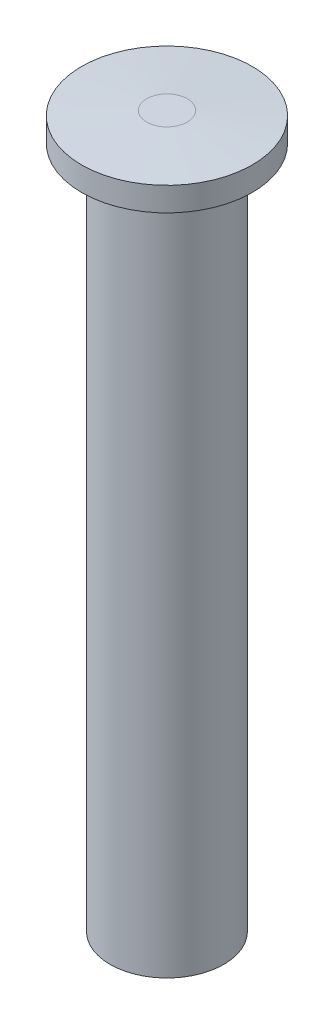
SolidWorks part; units mm, degrees
ref_plane "Front Plane" through (0, 0, 0) normal (0, 0, 1) x (1, 0, 0)
ref_plane "Top Plane" through (0, 0, 0) normal (0, 1, 0) x (1, 0, 0)
ref_plane "Right Plane" through (0, 0, 0) normal (1, 0, 0) x (0, 0, -1)
sketch "Sketch1" plane through (0, 0, 0) normal (0, 1, 0) x (1, 0, 0)
  circle A0 centre (0, 0) radius 3.175
  dimension "D1" = 6.35
extrude "Boss-Extrude1" add sketch "Sketch1" along normal mid plane 38.1
sketch "Sketch2" plane through (0, 19.05, 0) normal (0, 1, 0) x (1, 0, 0)
  circle A0 centre (0, 0) radius 4.7625
  dimension "D1" = 9.525
extrude "Boss-Extrude2" add sketch "Sketch2" along normal blind 1.5875
chamfer "Chamfer1" distance 0.254 angle 86 1 edges at (0, 20.6375, 4.7625)
